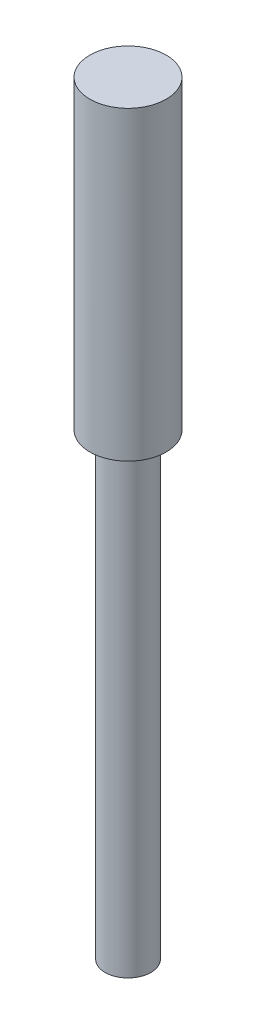
SolidWorks part; units mm, degrees
ref_plane "Front" through (0, 0, 0) normal (0, 0, 1) x (1, 0, 0)
ref_plane "Top" through (0, 0, 0) normal (0, 1, 0) x (1, 0, 0)
ref_plane "Right" through (0, 0, 0) normal (1, 0, 0) x (0, 0, -1)
sketch "Sketch1" plane through (0, 0, 0) normal (0, 1, 0) x (1, 0, 0)
  circle A0 centre (0, 0) radius 5
  dimension "D1" = 10
extrude "Boss-Extrude1" add sketch "Sketch1" along normal blind 100
sketch "Sketch2" plane through (0, 0, 0) normal (0, -1, 0) x (-1, 0, 0)
  circle A0 centre (0, 0) radius 3
  circle A1 centre (0, 0) radius 5
  circle A2 centre (0, 0) radius 5 construction
  dimension "D1" = 6
extrude "Cut-Extrude1" cut sketch "Sketch2" against normal blind 60
